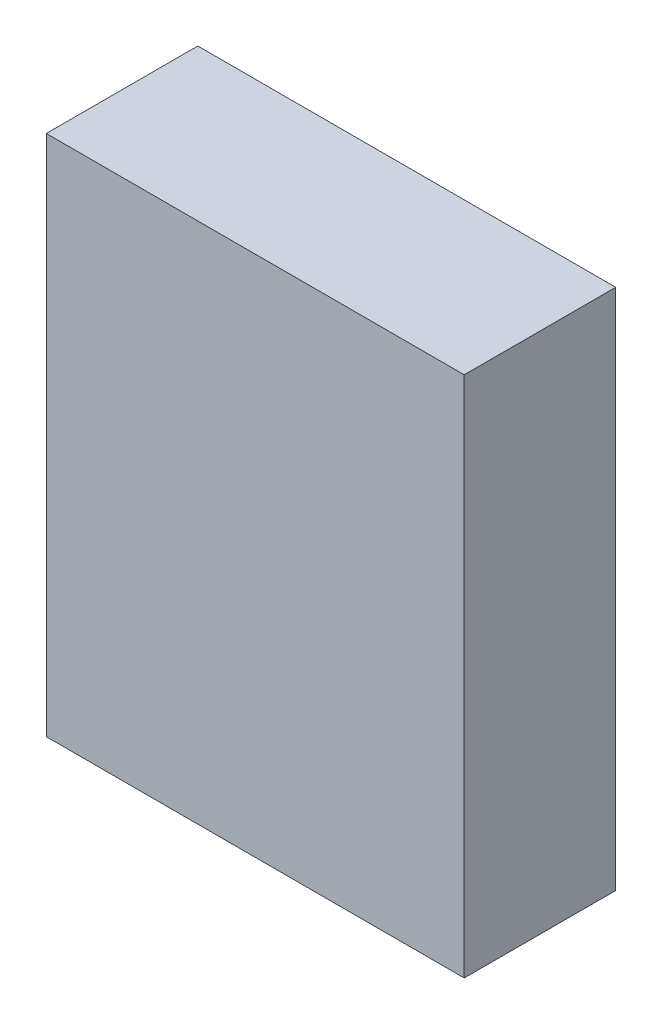
SolidWorks part; units mm, degrees
ref_plane "Front Plane" through (0, 0, 0) normal (0, 0, 1) x (1, 0, 0)
ref_plane "Top Plane" through (0, 0, 0) normal (0, 1, 0) x (1, 0, 0)
ref_plane "Right Plane" through (0, 0, 0) normal (1, 0, 0) x (0, 0, -1)
sketch "Sketch1" plane through (0, 0, 0) normal (0, 0, 1) x (1, 0, 0)
  line L1 (-40, -50) -> (40, -50)
  line L2 (-40, -50) -> (-40, 50)
  line L3 (-40, 50) -> (40, 50)
  line L4 (40, -50) -> (40, 50)
  line L5 (-40, -50) -> (40, 50) construction
  line L6 (-40, 50) -> (40, -50) construction
  point P0 (0, 0)
  dimension "D1" = 100
  dimension "D2" = 80
extrude "Boss-Extrude1" add sketch "Sketch1" along normal blind 29
